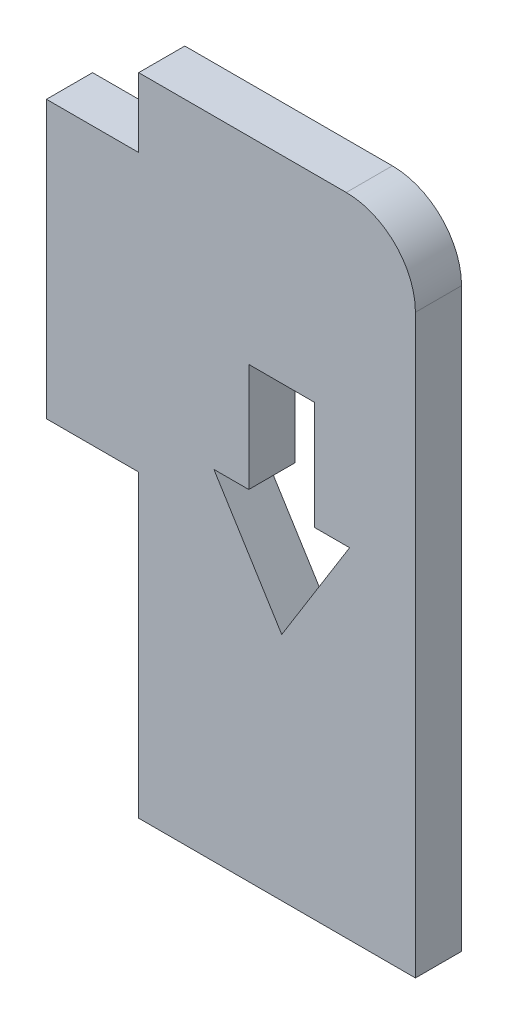
SolidWorks part; units mm, degrees
material "ﾊﾞﾙｻ"
ref_plane "正面" through (0, 0, 0) normal (0, 0, 1) x (1, 0, 0)
ref_plane "平面" through (0, 0, 0) normal (0, 1, 0) x (1, 0, 0)
ref_plane "右側面" through (0, 0, 0) normal (1, 0, 0) x (0, 0, -1)
sketch "ｽｹｯﾁ1" plane through (0, 0, 0) normal (0, 0, 1) x (1, 0, 0)
  line L0 (0, 0) -> (0, -12)
  line L1 (0, -12) -> (4, -12)
  line L2 (4, -12) -> (4, -35)
  line L3 (4, -35) -> (16, -35)
  line L4 (16, -35) -> (16, 3)
  line L5 (16, 3) -> (4, 3)
  line L6 (4, 3) -> (4, 0)
  line L7 (4, 0) -> (0, 0)
  line L8 (4, -25) -> (16, -25)
  dimension "D1" = 12
  dimension "D2" = 4
  dimension "D3" = 3
  dimension "D4" = 12
  dimension "D5" = 23
  dimension "D6" = 13
extrude "ﾎﾞｽ - 押し出し1" add sketch "ｽｹｯﾁ1" along normal blind 2 contours L2 L8 L4 L5 L6 L7 L0 L1
sketch "ｽｹｯﾁ2" plane through (0, 0, 2) normal (0, 0, 1) x (1, 0, 0)
  line L0 (10.2029, -4.1401) -> (10.2029, -16.3526) construction
  line L1 (11.6328, -5.5701) -> (8.7729, -5.5701)
  line L2 (8.7729, -5.5701) -> (8.7729, -10.2686)
  line L3 (8.7729, -10.2686) -> (7.2608, -10.2686)
  line L4 (7.2608, -10.2686) -> (10.2029, -15)
  line L5 (13.145, -10.2686) -> (10.2029, -15)
  line L6 (11.6328, -10.2686) -> (13.145, -10.2686)
  line L7 (11.6328, -5.5701) -> (11.6328, -10.2686)
  line L8 (16, -25) -> (16, 3) construction
  line L9 (16, 3) -> (4, 3) construction
  point P2 (7.2608, -10.2686)
  point P10 (10.2029, -5.5701)
  dimension "D1" = 2.855
  dimension "D2" = 4.3672
  dimension "D3" = 5.7971
  dimension "D4" = 8.5701
  dimension "D5" = 13.2686
  dimension "D6" = 18
extrude "ｶｯﾄ - 押し出し1" cut sketch "ｽｹｯﾁ2" against normal blind 2
fillet "ﾌｨﾚｯﾄ1" radius 3 1 edges at (16, 3, 1)
